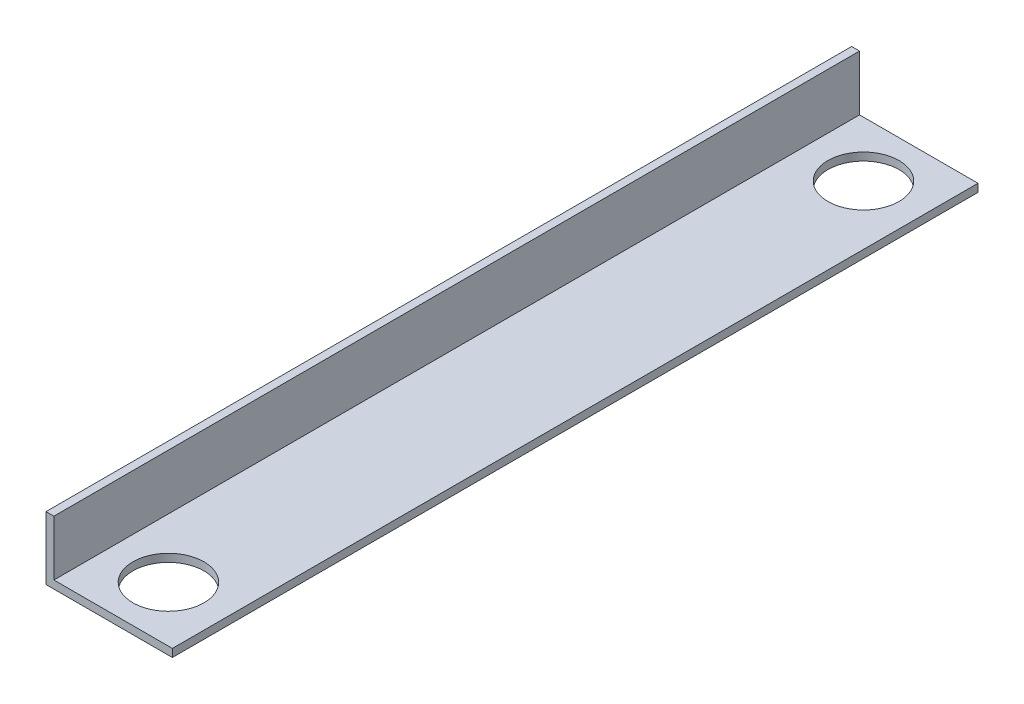
SolidWorks part; units mm, degrees
material "1060 Alloy"
ref_plane "Front Plane" through (0, 0, 0) normal (0, 0, 1) x (1, 0, 0)
ref_plane "Top Plane" through (0, 0, 0) normal (0, 1, 0) x (1, 0, 0)
ref_plane "Right Plane" through (0, 0, 0) normal (1, 0, 0) x (0, 0, -1)
sketch "Sketch1" plane through (0, 0, 0) normal (0, 0, 1) x (1, 0, 0)
  line L1 (0, 0) -> (50.8, 0)
  line L2 (0, 0) -> (0, 25.4)
  line L3 (0, 25.4) -> (3.175, 25.4)
  line L4 (50.8, 0) -> (50.8, 3.175)
  line L7 (50.8, 3.175) -> (3.175, 3.175)
  line L8 (3.175, 25.4) -> (3.175, 3.175)
  dimension "D1" = 25.4
  dimension "D2" = 50.8
  dimension "D3" = 3.175
extrude "Boss-Extrude1" add sketch "Sketch1" along normal blind 323.85
sketch "Sketch2" plane through (0, 3.175, 0) normal (0, 1, 0) x (1, 0, 0)
  line L0 (26.9875, -250.825) -> (26.9875, -73.025) construction
  line L1 (50.8, -161.925) -> (26.9875, -161.925) construction
  line L3 (50.8, -323.85) -> (50.8, 0) construction
  line L4 (26.9875, -161.925) -> (3.175, -161.925) construction
  line L5 (3.175, -323.85) -> (3.175, 0) construction
  circle A0 centre (26.9875, -301.625) radius 50.8 construction
  circle A1 centre (26.9875, -22.225) radius 50.8 construction
  circle A2 centre (26.9875, -301.625) radius 14.2875
  circle A3 centre (26.9875, -22.225) radius 14.2875
  dimension "D1" = 101.6
  dimension "D3" = 28.575
  dimension "D2" = 177.8
extrude "Cut-Extrude1" cut sketch "Sketch2" against normal through all
